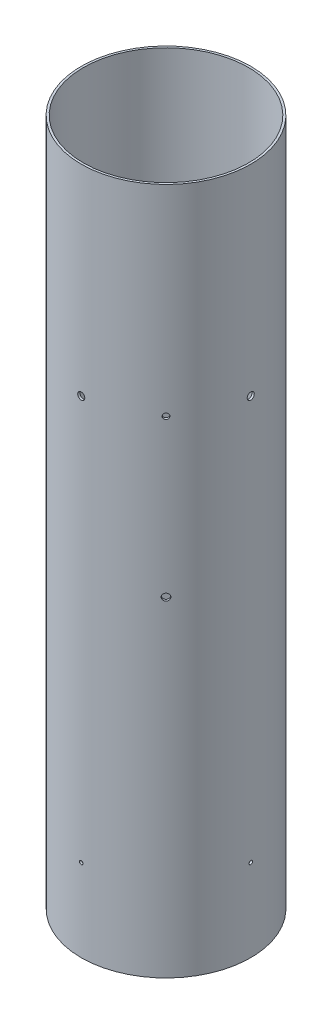
SolidWorks part; units mm, degrees
ref_plane "Front Plane" through (0, 0, 0) normal (0, 0, 1) x (1, 0, 0)
ref_plane "Top Plane" through (0, 0, 0) normal (0, 1, 0) x (1, 0, 0)
ref_plane "Right Plane" through (0, 0, 0) normal (1, 0, 0) x (0, 0, -1)
sketch "Sketch2" plane through (0, 0, 0) normal (0, 1, 0) x (1, 0, 0)
  circle A0 centre (0, 0) radius 76.3651
  circle A1 centre (0, 0) radius 78.359
  dimension "D1" = 152.7302
  dimension "D2" = 156.718
extrude "Boss-Extrude1" add sketch "Sketch2" along normal blind 635
ref_plane "Plane1" through (55.4082, 0, 55.4082) normal (0.7071, 0, 0.7071) x (0, -1, 0)
sketch "Sketch4" plane through (0, 0, 0) normal (0, 0, 1) x (1, 0, 0)
  circle A0 centre (0, 449.5038) radius 3.2639
  dimension "D2" = 6.5278
  dimension "D1" = 449.5038
extrude "Cut-Extrude2" cut sketch "Sketch4" against normal through all both and the other way through all
pattern_circular "CirPattern2" count 4 over 360 about axis through (0, 635, 0) along (0, 1, 0) of "Cut-Extrude2"
sketch "Sketch5" plane through (55.4082, 0, 55.4082) normal (0.7071, 0, 0.7071) x (0, -1, 0)
  circle A0 centre (-449.5038, 0) radius 2.5794
  dimension "D1" = 5.1587
  dimension "D2" = 449.5038
extrude "Cut-Extrude3" cut sketch "Sketch5" against normal up to surface and the other way through all up to face at (-76.299, 448.7564, 3.1772)
sketch "Sketch6" plane through (189.1754, 0, -78.359) normal (-0.7071, 0, -0.7071) x (-0.7071, 0, 0.7071)
  circle A0 centre (189.1754, 304.8) radius 3.175
  dimension "D2" = 304.8
extrude "Vent Hole" cut sketch "Sketch6" along normal up to surface (2.0599 mm away)
ref_plane "Plane2" through (0, 0, 78.359) normal (0, 0, 1) x (1, 0, 0)
sketch "Sketch7" plane through (0, 0, 78.359) normal (0, 0, 1) x (1, 0, 0)
  point P0 (0, 76.2)
  dimension "D1" = 76.2
hole_wizard "#4 Clearance Hole1" positions "Sketch7" profile "Sketch8" hole size "#4" standard "ANSI Inch" end condition through all
sketch "Sketch8" plane through (0, 76.2, 78.359) normal (1, 0, 0) x (0, -1, 0)
  line L0 (0, 0) -> (0, 156.718)
  line L1 (0, 156.718) -> (1.6319, 156.718)
  line L2 (1.6319, 156.718) -> (1.6319, 0)
  line L5 (1.6319, 0) -> (0, 0)
  line L11 (0, -6.35) -> (0, 107.95) construction
  dimension "Thru Hole Dia." = 3.2639
  dimension "Thru Hole Depth" = 156.718
pattern_circular "CirPattern3" count 2 every 90 about axis through (0, 0, 0) along (0, 1, 0) of "#4 Clearance Hole1"
equation "\"Shear Pin Dia\"= 3 / 32"
equation "\"Shear Pin Offset\"= 3"
equation "\"Bulkhead Screw Dia\"= 0.257"
equation "\"Bulkhead Screw Offset\"= 17.697"
equation "\"D1@Sketch4\"=\"Bulkhead Screw Offset\""
equation "\"D2@Sketch4\"=\"Bulkhead Screw Dia\""
equation "\"Rail Button Offset\"= 17.697"
equation "\"Rail Button Dia\"=0.2031"
equation "\"D1@Sketch5\"=\"Rail Button Dia\""
equation "\"Vent Hole Dia\"= 0.25"
equation "\"Vent Hole Offset\"= 12"
equation "\"D2@Sketch6\"=\"Vent Hole Offset\""
equation "\"D1@Sketch7\"=\"Shear Pin Offset\""
